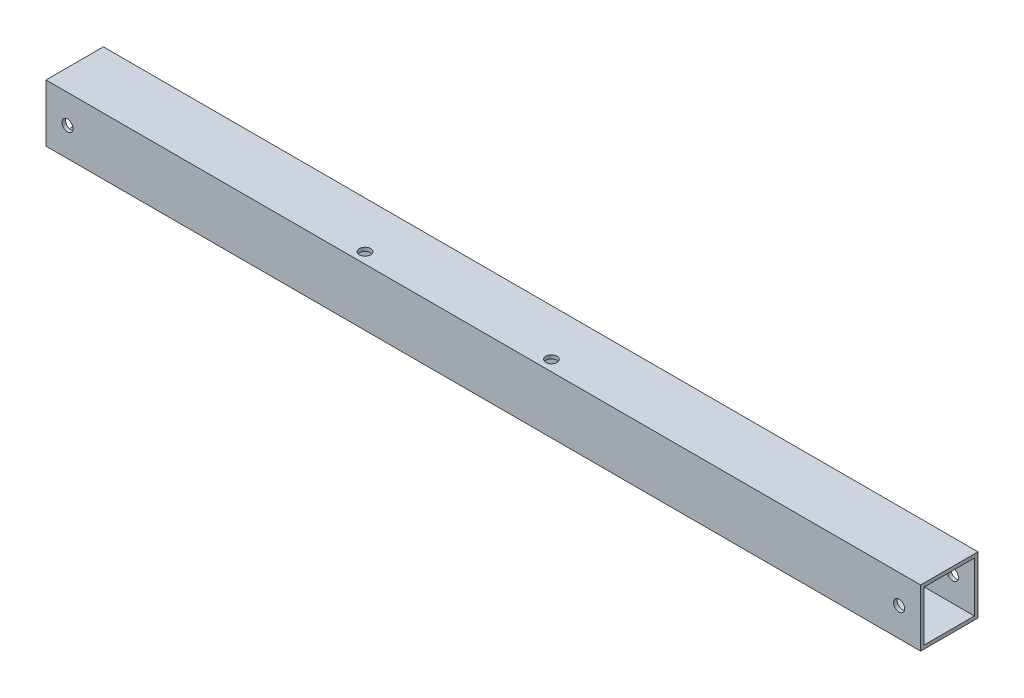
SolidWorks part; units mm, degrees
material "6061-T6 (SS)"
ref_plane "Front" through (0, 0, 0) normal (0, 0, 1) x (1, 0, 0)
ref_plane "Top" through (0, 0, 0) normal (0, 1, 0) x (1, 0, 0)
ref_plane "Right" through (0, 0, 0) normal (1, 0, 0) x (0, 0, -1)
sketch "Sketch1" plane through (0, 0, 0) normal (1, 0, 0) x (0, 0, -1)
  line L1 (-12.7, -12.7) -> (12.7, -12.7)
  line L2 (-12.7, -12.7) -> (-12.7, 12.7)
  line L3 (-12.7, 12.7) -> (12.7, 12.7)
  line L4 (12.7, -12.7) -> (12.7, 12.7)
  line L5 (-12.7, -12.7) -> (12.7, 12.7) construction
  line L6 (-12.7, 12.7) -> (12.7, -12.7) construction
  point P0 (0, 0)
  dimension "D1" = 25.4
extrude "Extrude-Thin1" add sketch "Sketch1" along normal blind 387.35 thin thin type one direction reverse wall 1.5875
sketch "Sketch4" plane through (0, 0, 12.7) normal (0, 0, 1) x (1, 0, 0)
  line L0 (0, 12.7) -> (0, -12.7) construction
  line L1 (387.35, 12.7) -> (387.35, -12.7) construction
  point P0 (9.525, 0)
  point P2 (377.825, 0)
  dimension "D1" = 9.525
  dimension "D2" = 9.525
hole_wizard "#10 (0.1935) Diameter Hole1" positions "Sketch4" profile "Sketch3" hole size "#10" standard "ANSI Inch" end condition through all
sketch "Sketch3" plane through (9.525, 0, 12.7) normal (1, 0, 0) x (0, -1, 0)
  line L0 (0, 0) -> (0, 25.4)
  line L1 (0, 25.4) -> (2.4574, 25.4)
  line L2 (2.4574, 25.4) -> (2.4574, 0)
  line L5 (2.4574, 0) -> (0, 0)
  line L11 (0, -6.35) -> (0, 107.95) construction
  dimension "Thru Hole Dia." = 4.9149
  dimension "Thru Hole Depth" = 25.4
sketch "Sketch7" plane through (0, 12.7, 0) normal (0, 1, 0) x (1, 0, 0)
  line L0 (387.35, -12.7) -> (0, -12.7) construction
  line L1 (0, 12.7) -> (0, -12.7) construction
  point P0 (136.525, -7.9375)
  point P2 (219.075, -7.9375)
  dimension "D1" = 4.7625
  dimension "D2" = 136.525
  dimension "D3" = 82.55
hole_wizard "#10 (0.1935) Diameter Hole2" positions "Sketch7" profile "Sketch6" hole size "#10" standard "ANSI Inch" end condition through all
sketch "Sketch6" plane through (136.525, 12.7, 7.9375) normal (1, 0, 0) x (0, 0, 1)
  line L0 (0, 0) -> (0, 25.4)
  line L1 (0, 25.4) -> (2.4574, 25.4)
  line L2 (2.4574, 25.4) -> (2.4574, 0)
  line L5 (2.4574, 0) -> (0, 0)
  line L11 (0, -6.35) -> (0, 107.95) construction
  dimension "Thru Hole Dia." = 4.9149
  dimension "Thru Hole Depth" = 25.4
